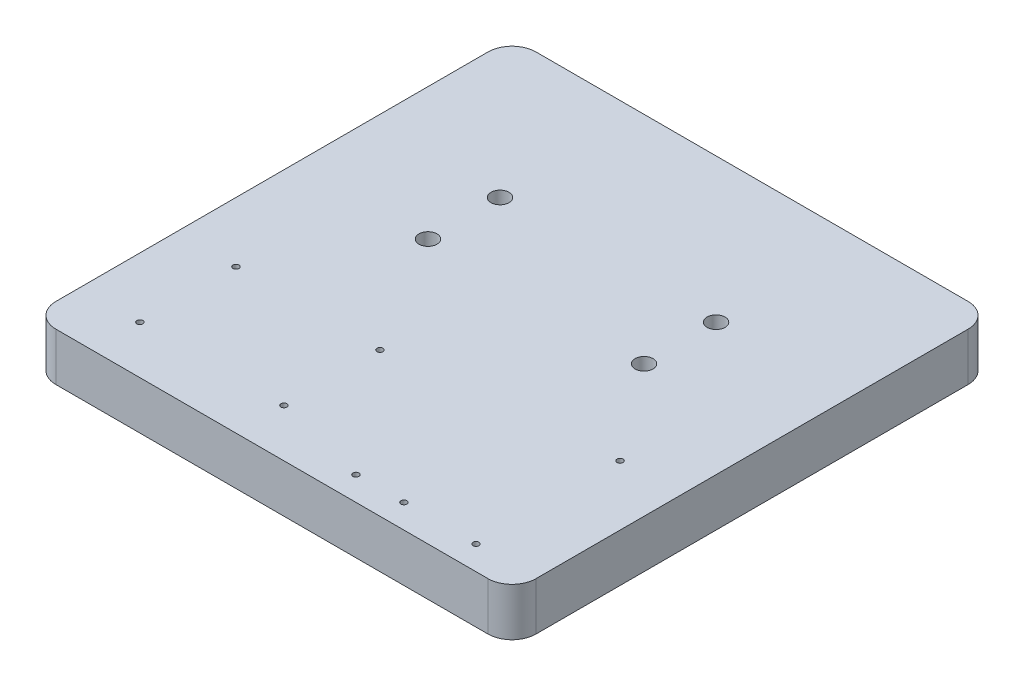
SolidWorks part; units mm, degrees
ref_plane "Alzado" through (0, 0, 0) normal (0, 0, 1) x (1, 0, 0)
ref_plane "Planta" through (0, 0, 0) normal (0, 1, 0) x (1, 0, 0)
ref_plane "Vista lateral" through (0, 0, 0) normal (1, 0, 0) x (0, 0, -1)
sketch "Croquis1" plane through (0, 0, 0) normal (0, 1, 0) x (1, 0, 0)
  line L1 (-100, -100) -> (100, -100)
  line L2 (-100, -100) -> (-100, 100)
  line L3 (-100, 100) -> (100, 100)
  line L4 (100, -100) -> (100, 100)
  line L5 (-100, -100) -> (100, 100) construction
  line L6 (-100, 100) -> (100, -100) construction
  point P0 (0, 0)
  dimension "D1" = 200
  dimension "D2" = 200
extrude "Saliente-Extruir1" add sketch "Croquis1" along normal blind 20
ref_plane "Plano2" through (0, 0, -25) normal (0, 0, 1) x (1, 0, 0)
sketch "Croquis2" plane through (0, 20, 0) normal (0, 1, 0) x (1, 0, 0)
  line L1 (-100, -100) -> (100, -100) construction
  line L2 (-100, 100) -> (-100, -100) construction
  circle A0 centre (-85, -5) radius 1.6
  circle A1 centre (-75, 5) radius 1.6
  dimension "D1" = 15
  dimension "D2" = 3.2
  dimension "D4" = 3.2
  dimension "D3" = 95
  dimension "D5" = 10
  dimension "D6" = 10
extrude "Cortar-Extruir1" [suppressed] cut sketch "Croquis2" against normal through all
pattern_linear "MatrizL1" [suppressed] count 9 spacing 20 count 5 spacing 20
fillet "Redondeo1" radius 10 4 edges at (-100, 10, 100) (100, 10, 100) (100, 10, -100) (-100, 10, -100)
sketch "Croquis5" plane through (0, 20, 0) normal (0, 1, 0) x (1, 0, 0)
  line L0 (100, -90) -> (100, 90) construction
  line L1 (60, -20) -> (-60, -20)
  line L2 (60, -20) -> (60, 60)
  line L3 (60, 60) -> (-60, 60)
  line L4 (-60, -20) -> (-60, 60)
  line L5 (90, 100) -> (-90, 100) construction
  point P6 (100, 0)
  dimension "D1" = 40
  dimension "D2" = 40
  dimension "D3" = 120
  dimension "D4" = 80
extrude "Saliente-Extruir3" add sketch "Croquis5" against normal blind 20
sketch "Croquis3" plane through (0, 20, 0) normal (0, 1, 0) x (1, 0, 0)
  line L0 (-11, 25) -> (11, 25) construction
  line L2 (0, 0) -> (0, 100) construction
  line L3 (90, 100) -> (-90, 100) construction
  circle A0 centre (-45, 10) radius 3.75
  circle A3 centre (45, 10) radius 3.75
  dimension "D1" = 7.5
  dimension "D2" = 15
  dimension "D3" = 45
extrude "Cortar-Extruir2" cut sketch "Croquis3" against normal through all
mirror "Simetría3" about plane through (0, 0, -25) normal (0, 0, 1) of "Cortar-Extruir2"
sketch "Croquis6" plane through (0, 20, 0) normal (0, 1, 0) x (1, 0, 0)
  line L1 (-90, -100) -> (90, -100) construction
  line L2 (-45, -100) -> (-45, -40) construction
  line L3 (-100, 90) -> (-100, -90) construction
  line L4 (100, -90) -> (100, 90) construction
  circle A0 centre (75, -90) radius 1.25
  circle A1 centre (75, -30) radius 1.25
  circle A2 centre (45, -90) radius 1.25
  circle A3 centre (25, -90) radius 1.25
  circle A4 centre (-15, -80) radius 1.25
  circle A5 centre (-15, -40) radius 1.25
  circle A6 centre (-75, -40) radius 1.25
  circle A7 centre (-75, -80) radius 1.25
  dimension "D1" = 2.5
  dimension "D4" = 2.5
  dimension "D6" = 2.5
  dimension "D8" = 2.5
  dimension "D10" = 2.5
  dimension "D13" = 2.5
  dimension "D2" = 25
  dimension "D3" = 10
  dimension "D5" = 60
  dimension "D7" = 30
  dimension "D9" = 20
  dimension "D11" = 20
  dimension "D12" = 25
  dimension "D14" = 40
  dimension "D15" = 30
extrude "Cortar-Extruir3" cut sketch "Croquis6" against normal through all
